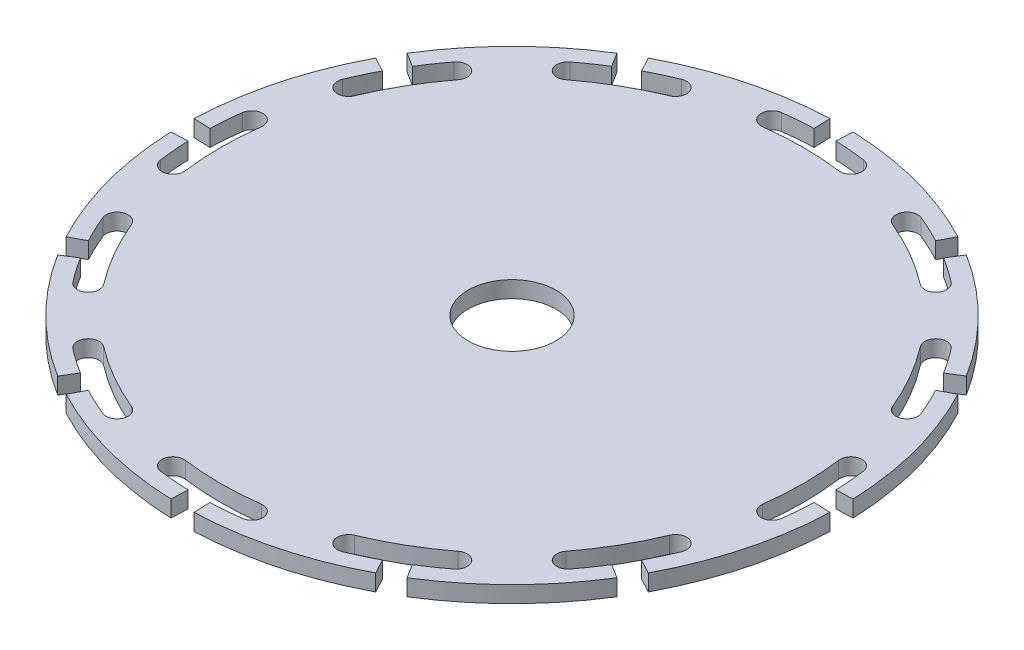
SolidWorks part; units mm, degrees
material "6061 Alloy"
ref_plane "Front Plane" through (0, 0, 0) normal (0, 0, 1) x (1, 0, 0)
ref_plane "Top Plane" through (0, 0, 0) normal (0, 1, 0) x (1, 0, 0)
ref_plane "Right Plane" through (0, 0, 0) normal (1, 0, 0) x (0, 0, -1)
sketch "Sketch1" plane through (0, 0, 0) normal (0, 1, 0) x (1, 0, 0)
  circle A0 centre (0, 0) radius 30
  dimension "D1" = 60
sketch "Sketch2" plane through (0, 0, 0) normal (0, 1, 0) x (1, 0, 0)
  line L0 (0, 0) -> (0, 30) construction
  line L1 (-1.047, 29.9817) -> (0, 0) construction
  line L2 (0, 0) -> (-3.9158, 29.7433) construction
  line L3 (-1.047, 29.9817) -> (-0.9946, 28.4826)
  line L4 (0, 0) -> (3.9158, 29.7433) construction
  line L5 (1.047, 29.9817) -> (0, 0) construction
  line L6 (1.047, 29.9817) -> (0.9946, 28.4826)
  arc A0 (3.4589, 26.2733) -> (-3.4589, 26.2733) centre (0, 0) ccw
  circle A1 centre (0, 0) radius 30 construction
  arc A2 (-1.047, 29.9817) -> (1.047, 29.9817) centre (0, 0) cw
  arc A3 (-0.9946, 28.4826) -> (-3.72, 28.2562) centre (0, 0) ccw
  arc A4 (-3.4589, 26.2733) -> (-3.72, 28.2562) centre (-3.5895, 27.2647) cw
  arc A5 (3.4589, 26.2733) -> (3.72, 28.2562) centre (3.5895, 27.2647) ccw
  arc A6 (0.9946, 28.4826) -> (3.72, 28.2562) centre (0, 0) cw
  point P130 (0, 0)
  dimension "D1" = 15
  dimension "D2" = 2
  dimension "D4" = 1.5
  dimension "D3" = 4
sketch "Sketch3" plane through (0, 0, 0) normal (0, 1, 0) x (1, 0, 0)
  circle A0 centre (0, 0) radius 4
  dimension "D1" = 8
extrude "Wheel Blank" add sketch "Sketch1" along normal blind 1.5
extrude "T-Slot" cut sketch "Sketch2" along normal through all
pattern_circular "CirPattern1" count 12 over 360 about axis through (0, 0, 0) along (0, 1, 0) of "T-Slot"
extrude "Center Hole" cut sketch "Sketch3" along normal blind 6
